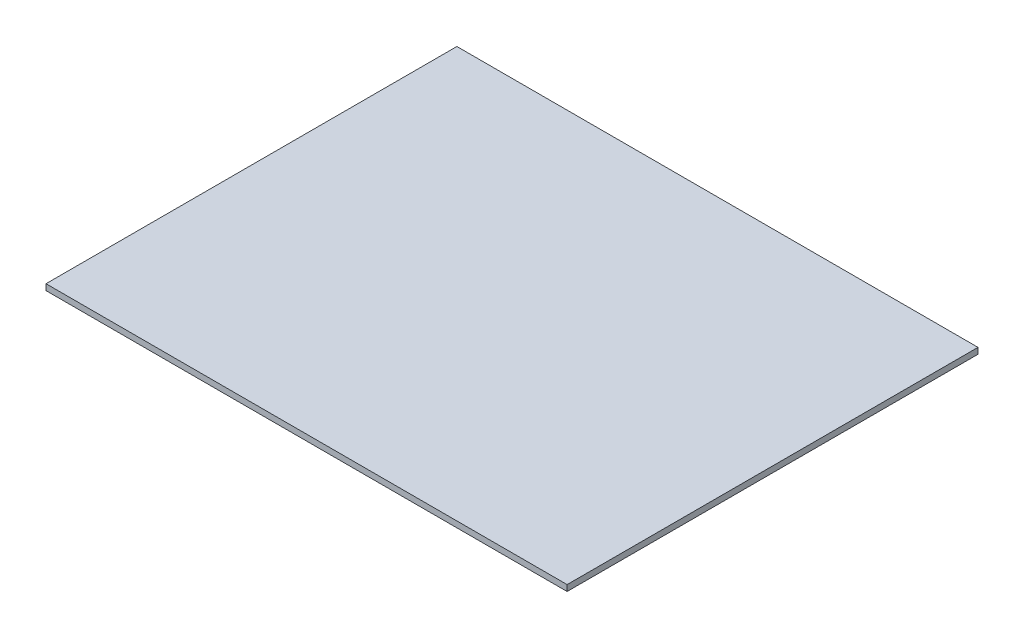
SolidWorks part; units mm, degrees
material "Balsa"
ref_plane "Front Plane" through (0, 0, 0) normal (0, 0, 1) x (1, 0, 0)
ref_plane "Top Plane" through (0, 0, 0) normal (0, 1, 0) x (1, 0, 0)
ref_plane "Right Plane" through (0, 0, 0) normal (1, 0, 0) x (0, 0, -1)
sketch "Sketch1" plane through (0, 0, 0) normal (0, 1, 0) x (1, 0, 0)
  line L1 (-141.2847, 77.8646) -> (118.7153, 77.8646)
  line L2 (-141.2847, 77.8646) -> (-141.2847, -127.1354)
  line L3 (-141.2847, -127.1354) -> (118.7153, -127.1354)
  line L4 (118.7153, 77.8646) -> (118.7153, -127.1354)
  dimension "D1" = 260
  dimension "D2" = 205
extrude "Boss-Extrude1" add sketch "Sketch1" along normal blind 3
